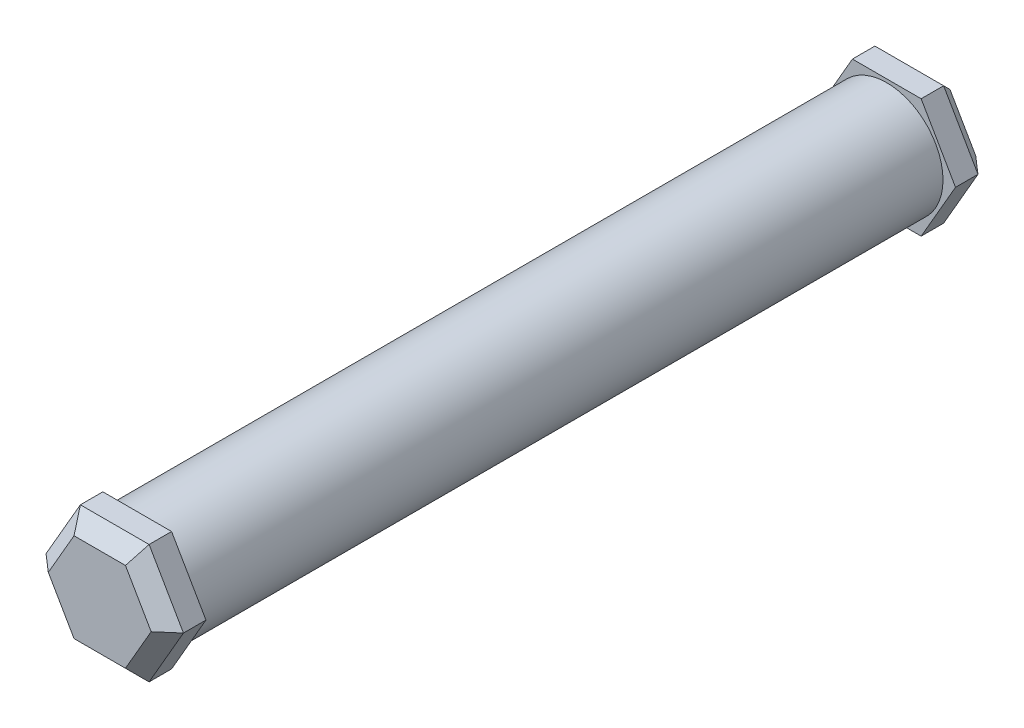
SolidWorks part; units mm, degrees
ref_plane "Front Plane" through (0, 0, 0) normal (0, 0, 1) x (1, 0, 0)
ref_plane "Top Plane" through (0, 0, 0) normal (0, 1, 0) x (1, 0, 0)
ref_plane "Right Plane" through (0, 0, 0) normal (1, 0, 0) x (0, 0, -1)
sketch "Sketch1" plane through (0, 0, 0) normal (0, 0, 1) x (1, 0, 0)
  circle A0 centre (0, 0) radius 15
  dimension "D1" = 30
extrude "Boss-Extrude1" add sketch "Sketch1" along normal blind 200
sketch "Sketch2" plane through (0, 0, 200) normal (0, 0, 1) x (1, 0, 0)
  line L1 (18.3387, 0) -> (9.1693, 15.8817)
  line L2 (9.1693, 15.8817) -> (-9.1693, 15.8817)
  line L3 (-9.1693, 15.8817) -> (-18.3387, 0)
  line L4 (-18.3387, 0) -> (-9.1693, -15.8817)
  line L5 (-9.1693, -15.8817) -> (9.1693, -15.8817)
  line L6 (9.1693, -15.8817) -> (18.3387, 0)
  circle A0 centre (0, 0) radius 15.8817 construction
sketch "Sketch3" plane through (0, 0, 0) normal (0, 0, -1) x (-1, 0, 0)
  line L1 (18.3387, 0) -> (9.1693, 15.8817)
  line L2 (9.1693, 15.8817) -> (-9.1693, 15.8817)
  line L3 (-9.1693, 15.8817) -> (-18.3387, 0)
  line L4 (-18.3387, 0) -> (-9.1693, -15.8817)
  line L5 (-9.1693, -15.8817) -> (9.1693, -15.8817)
  line L6 (9.1693, -15.8817) -> (18.3387, 0)
  circle A0 centre (0, 0) radius 15.8817 construction
extrude "Boss-Extrude2" add sketch "Sketch3" along normal blind 10
extrude "Boss-Extrude3" add sketch "Sketch2" along normal blind 10 contours L1 L2 L3 L4 L5 L6
chamfer "Chamfer1" distance 4 angle 45 12 edges at (0, -15.8817, -10) (13.754, -7.9409, -10) (13.754, 7.9409, -10) (0, 15.8817, -10) (-13.754, 7.9409, -10) (-13.754, -7.9409, -10) (0, -15.8817, 210) (-13.754, -7.9409, 210) (-13.754, 7.9409, 210) (0, 15.8817, 210) (13.754, 7.9409, 210) (13.754, -7.9409, 210)
